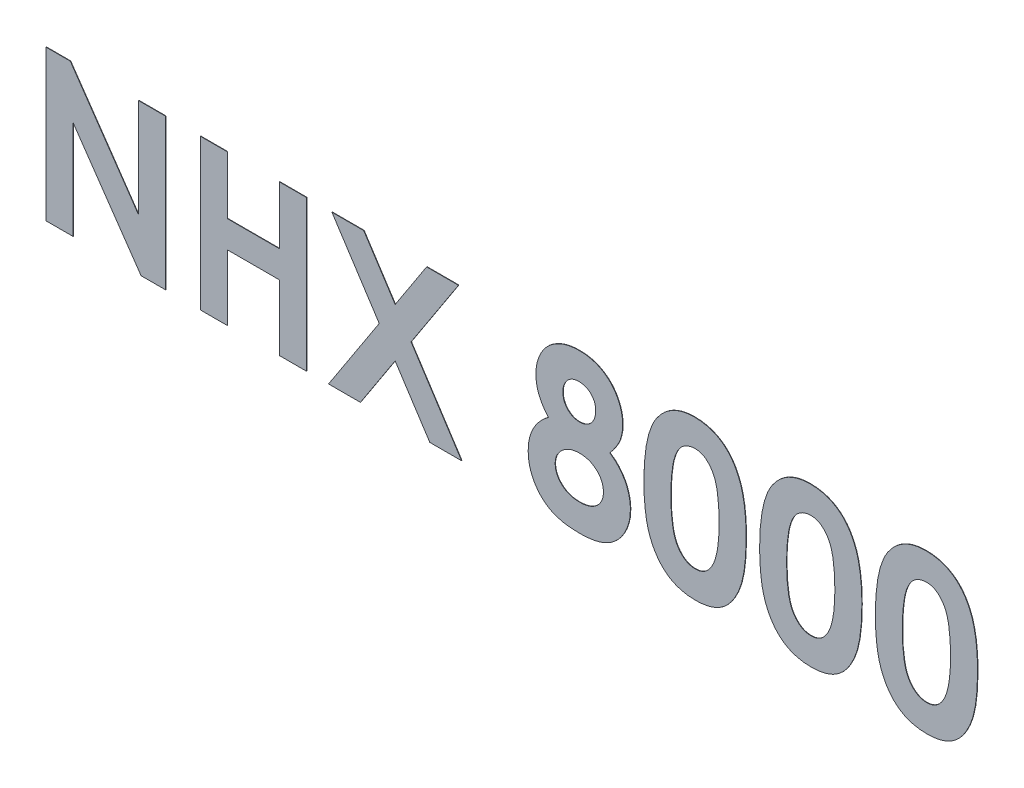
SolidWorks part; units mm, degrees
ref_plane "Piano frontale" through (0, 0, 0) normal (0, 0, 1) x (1, 0, 0)
ref_plane "Piano superiore" through (0, 0, 0) normal (0, 1, 0) x (1, 0, 0)
ref_plane "Piano destro" through (0, 0, 0) normal (1, 0, 0) x (0, 0, -1)
sketch "Schizzo1" plane through (0, 0, 0) normal (0, 0, 1) x (1, 0, 0)
  text T0 "<b>NHX 8000</b>" font "Century Gothic" height 3.5
extrude "Estrusione-Estrusione1" add sketch "Schizzo1" along normal blind 0.01
scale "Scala1" bodies to scale 107 106 105 104 103 102 101 scale about origin uniform scaling yes scale factor 40
